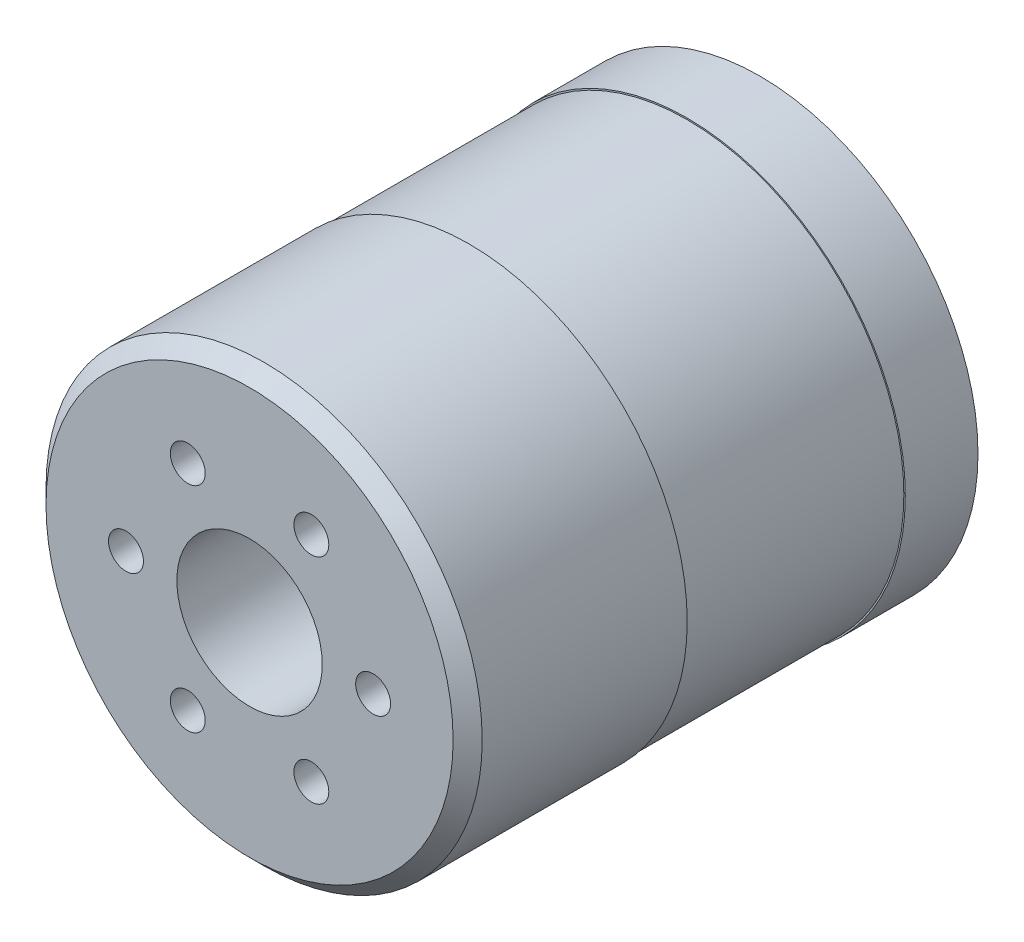
SolidWorks part; units mm, degrees
ref_plane "Face" through (0, 0, 0) normal (0, 0, 1) x (1, 0, 0)
ref_plane "Dessus" through (0, 0, 0) normal (0, 1, 0) x (1, 0, 0)
ref_plane "Droite" through (0, 0, 0) normal (1, 0, 0) x (0, 0, -1)
sketch "Esquisse1" plane through (0, 0, 0) normal (0, 0, 1) x (1, 0, 0)
  circle A0 centre (0, 0) radius 15
  dimension "D1" = 30
extrude "Extrusion1" add sketch "Esquisse1" along normal blind 35.1
sketch "Esquisse2" plane through (0, 0, 0) normal (0, 0, -1) x (-1, 0, 0)
  circle A0 centre (0, 0) radius 9
  dimension "D1" = 18
extrude "Extrusion2" add sketch "Esquisse2" along normal blind 4
sketch "Esquisse3" plane through (0, 0, -4) normal (0, 0, -1) x (-1, 0, 0)
  circle A0 centre (0, 0) radius 5
  dimension "D1" = 10
extrude "Extrusion3" add sketch "Esquisse3" along normal blind 0.5
chamfer "Chanfrein1" distance 1 angle 45 1 edges at (15, 0, 35.1)
sketch "Esquisse7" plane through (0, 0, 0) normal (0, 0, -1) x (-1, 0, 0)
  circle A0 centre (0, 0) radius 4
  dimension "D1" = 8
extrude "Enlèv. mat.-Extru.1" cut sketch "Esquisse7" along normal up to next
sketch "Esquisse8" plane through (0, 0, 0) normal (0, 0, -1) x (-1, 0, 0)
  circle A0 centre (0, 0) radius 15
  circle A1 centre (0, 0) radius 14.9
  circle A2 centre (0, 0) radius 15 construction
  dimension "D1" = 0.1
extrude "Enlèv. mat.-Extru.2" cut sketch "Esquisse8" against normal blind 20
sketch "Esquisse9" plane through (0, 0, 0) normal (0, 0, -1) x (-1, 0, 0)
  circle A0 centre (0, 0) radius 15
  circle A1 centre (0, 0) radius 15 construction
extrude "Extrusion4" add sketch "Esquisse9" against normal blind 5
hole_wizard "Trou taraudé M31" positions "Esquisse5" profile "Esquisse4" tap size "M3" standard "ISO"
sketch "Esquisse5" plane through (0, 0, 0) normal (0, 0, -1) x (-1, 0, 0)
  line L0 (0, 15) -> (0, -15) construction
  line L2 (15, 0) -> (-15, 0) construction
  circle A0 centre (0, 0) radius 15 construction
  circle A1 centre (0, 0) radius 13
  point P0 (13, 0)
  point P14 (0, 13)
  point P16 (-13, 0)
  point P18 (0, -13)
  dimension "D1" = 26
sketch "Esquisse4" plane through (-13, 0, 0) normal (1, 0, 0) x (0, 1, 0)
  line L0 (0, 0) -> (0, 5.2511)
  line L1 (0, 5.2511) -> (1.25, 4.5)
  line L2 (1.25, 4.5) -> (1.25, 0)
  line L5 (1.25, 0) -> (0, 0)
  line L10 (0, 5.2511) -> (-1.25, 4.5) construction
  line L11 (0, -6.35) -> (0, 107.95) construction
  dimension "Diamètre du trou pour taraudage" = 2.5
  dimension "Profondeur du trou pour taraudage" = 4.5
  dimension "Angle de pointe" = 118
cosmetic thread "Filetage de perçage1" parameters "D1"=3, "D2"=3
cosmetic thread "Filetage de perçage2" parameters "D1"=3, "D2"=3
cosmetic thread "Filetage de perçage3" parameters "D1"=3, "D2"=3
cosmetic thread "Filetage de perçage4" parameters "D1"=3, "D2"=3
sketch "Esquisse10" plane through (0, 0, 35.1) normal (0, 0, 1) x (1, 0, 0)
  circle A0 centre (0, 0) radius 5
  dimension "D1" = 10
extrude "Enlèv. mat.-Extru.3" cut sketch "Esquisse10" against normal blind 15
hole_wizard "Dégagement M21" positions "Esquisse13" profile "Esquisse14" hole size "M2" standard "Ansi Métrique"
sketch "Esquisse13" plane through (0, 0, 35.1) normal (0, 0, 1) x (1, 0, 0)
  line L0 (8.5, 0) -> (-8.5, 0) construction
  line L2 (-4.25, 7.3612) -> (4.25, -7.3612) construction
  line L4 (4.25, 7.3612) -> (-4.25, -7.3612) construction
  circle A0 centre (0, 0) radius 8.5
  point P0 (4.25, -7.3612)
  point P19 (-4.25, -7.3612)
  point P21 (-8.5, 0)
  point P23 (-4.25, 7.3612)
  point P25 (4.25, 7.3612)
  point P27 (8.5, 0)
  dimension "D1" = 17
  dimension "D2" = 60
  dimension "D3" = 60
sketch "Esquisse14" plane through (4.25, -7.3612, 35.1) normal (1, 0, 0) x (0, -1, 0)
  line L0 (0, 0) -> (0, 3.721)
  line L1 (0, 3.721) -> (1.2, 3)
  line L2 (1.2, 3) -> (1.2, 0)
  line L5 (1.2, 0) -> (0, 0)
  line L10 (0, 3.721) -> (-1.2, 3) construction
  line L11 (0, -6.35) -> (0, 107.95) construction
  dimension "Diamètre du perçage" = 2.4
  dimension "Profondeur du perçage" = 3
  dimension "Angle de pointe" = 118
